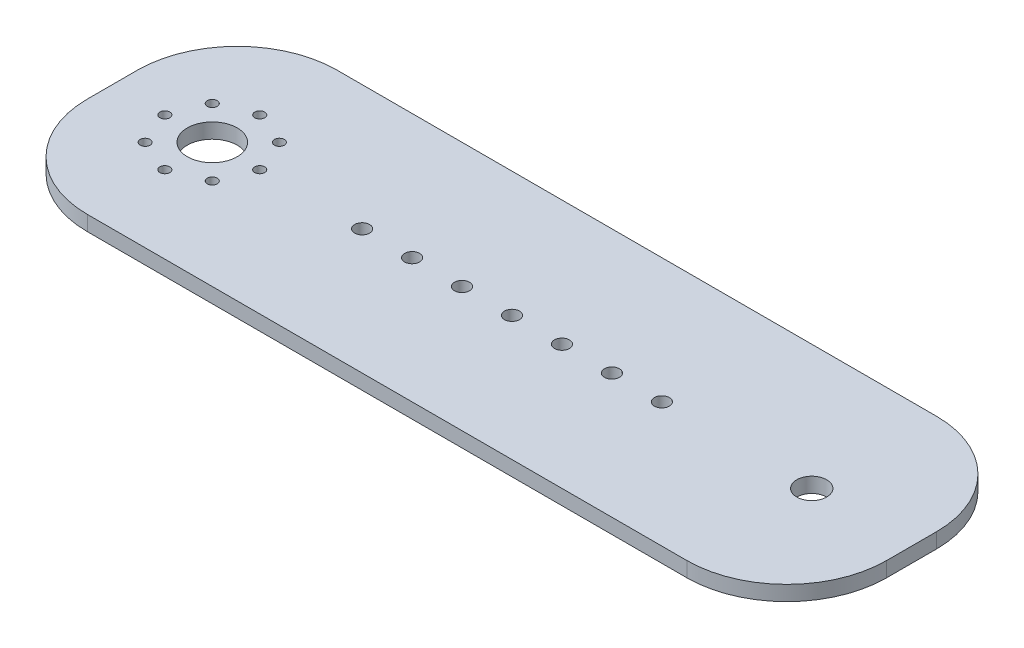
SolidWorks part; units mm, degrees
ref_plane "Front Plane" through (0, 0, 0) normal (0, 0, 1) x (1, 0, 0)
ref_plane "Top Plane" through (0, 0, 0) normal (0, 1, 0) x (1, 0, 0)
ref_plane "Right Plane" through (0, 0, 0) normal (1, 0, 0) x (0, 0, -1)
sketch "Sketch1" plane through (0, 0, 0) normal (0, 1, 0) x (1, 0, 0)
  line L1 (-80, 25) -> (80, 25)
  line L2 (-80, 25) -> (-80, -25)
  line L3 (-80, -25) -> (80, -25)
  line L4 (80, 25) -> (80, -25)
  line L5 (-80, 25) -> (80, -25) construction
  line L6 (-80, -25) -> (80, 25) construction
  point P0 (0, 0)
extrude "Boss-Extrude1" add sketch "Sketch1" along normal blind 3
fillet "Fillet1" radius 20 4 edges at (80, 1.5, -25) (80, 1.5, 25) (-80, 1.5, -25) (-80, 1.5, 25)
sketch "Sketch2" plane through (0, 3, 0) normal (0, 1, 0) x (1, 0, 0)
  line L1 (-80, 5) -> (-80, -5) construction
  circle A0 centre (-60, 0) radius 5
  dimension "D1" = 20
extrude "Cut-Extrude1" cut sketch "Sketch2" against normal through all
sketch "Sketch3" plane through (0, 3, 0) normal (0, 1, 0) x (1, 0, 0)
  circle A0 centre (-50.5, 0) radius 1
  circle A1 centre (-60, 0) radius 5 construction
  dimension "D2" = 2
  dimension "D1" = 9.5
extrude "Cut-Extrude2" cut sketch "Sketch3" against normal through all contours A0
pattern_circular "CirPattern1" count 8 every 45 about axis through (-60, 0, 0) along (0, 1, 0) of "Cut-Extrude2"
sketch "Sketch4" plane through (0, 3, 0) normal (0, 1, 0) x (1, 0, 0)
  line L0 (80, -5) -> (80, 5) construction
  circle A0 centre (60, 0) radius 3
  dimension "D1" = 20
extrude "Cut-Extrude3" cut sketch "Sketch4" against normal through all
sketch "Sketch5" plane through (0, 3, 0) normal (0, 1, 0) x (1, 0, 0)
  circle A0 centre (0, 0) radius 1.5
extrude "Cut-Extrude4" cut sketch "Sketch5" against normal through all
pattern_linear "LPattern1" count 4 spacing 10 along (1, 0, 0) count 4 spacing 10 along (-1, 0, 0) of "Cut-Extrude4"
